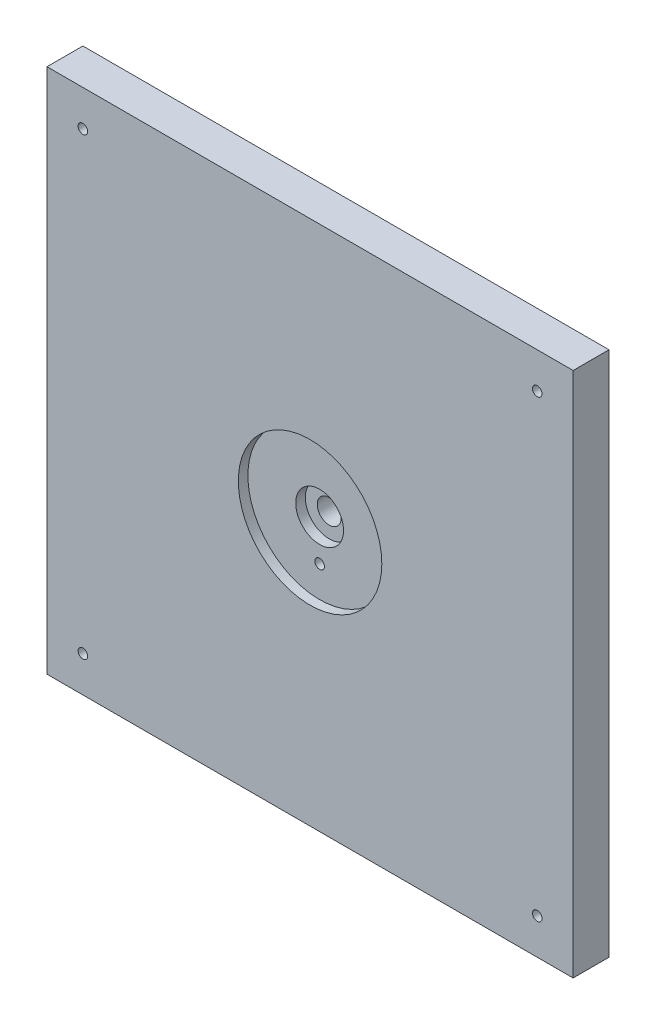
SolidWorks part; units mm, degrees
ref_plane "Front Plane" through (0, 0, 0) normal (0, 0, 1) x (1, 0, 0)
ref_plane "Top Plane" through (0, 0, 0) normal (0, 1, 0) x (1, 0, 0)
ref_plane "Right Plane" through (0, 0, 0) normal (1, 0, 0) x (0, 0, -1)
sketch "Sketch2" plane through (0, 0, 0) normal (0, 0, 1) x (1, 0, 0)
  line L1 (-139.7, 139.7) -> (139.7, 139.7)
  line L2 (-139.7, 139.7) -> (-139.7, -139.7)
  line L3 (-139.7, -139.7) -> (139.7, -139.7)
  line L4 (139.7, 139.7) -> (139.7, -139.7)
  dimension "D1" = 279.4
  dimension "D2" = 279.4
  dimension "D3" = 139.7
  dimension "D4" = 139.7
extrude "Boss-Extrude1" add sketch "Sketch2" along normal blind 19.05
sketch "Sketch6" plane through (0, 0, 19.05) normal (0, 0, 1) x (1, 0, 0)
  circle A0 centre (0, 0) radius 12.7
  dimension "D1" = 25.4
extrude "Cut-Extrude3" cut sketch "Sketch6" against normal blind 10.16
sketch "Sketch8" plane through (0, 0, 19.05) normal (0, 0, 1) x (1, 0, 0)
  circle A0 centre (0, 0) radius 38.1
  dimension "D1" = 76.2
extrude "Cut-Extrude4" cut sketch "Sketch8" against normal blind 5.08
sketch "Sketch9" plane through (0, 0, 8.89) normal (0, 0, 1) x (1, 0, 0)
  circle A0 centre (0, 0) radius 6.35
  dimension "D1" = 12.7
extrude "Cut-Extrude5" cut sketch "Sketch9" against normal blind 39.37 contours A0
sketch "Sketch10" plane through (0, 0, 19.05) normal (0, 0, 1) x (1, 0, 0)
  line L0 (-120.65, 120.65) -> (120.65, 120.65) construction
  line L1 (120.65, 120.65) -> (120.65, -120.65) construction
  line L2 (120.65, -120.65) -> (-120.65, -120.65) construction
  line L3 (-120.65, -120.65) -> (-120.65, 120.65) construction
  line L4 (-139.7, 139.7) -> (-139.7, -139.7) construction
  line L5 (139.7, 139.7) -> (-139.7, 139.7) construction
  line L6 (139.7, -139.7) -> (139.7, 139.7) construction
  line L7 (-139.7, -139.7) -> (139.7, -139.7) construction
  circle A0 centre (-120.65, -120.65) radius 2.54
  circle A1 centre (-120.65, 120.65) radius 2.54
  circle A2 centre (120.65, 120.65) radius 2.54
  circle A3 centre (120.65, -120.65) radius 2.54
  dimension "D5" = 5.08
  dimension "D6" = 5.08
  dimension "D7" = 5.08
  dimension "D8" = 5.08
  dimension "D1" = 19.05
  dimension "D2" = 19.05
  dimension "D3" = 19.05
  dimension "D4" = 19.05
extrude "Cut-Extrude6" cut sketch "Sketch10" against normal blind 39.37
sketch "Sketch11" plane through (0, 0, 19.05) normal (0, 0, 1) x (1, 0, 0)
  line L0 (-139.7, 139.7) -> (-139.7, -139.7) construction
  circle A0 centre (0, -21.59) radius 2.54
  dimension "D1" = 5.08
  dimension "D2" = 21.59
  dimension "D3" = 139.7
extrude "Cut-Extrude7" cut sketch "Sketch11" against normal blind 36.576
